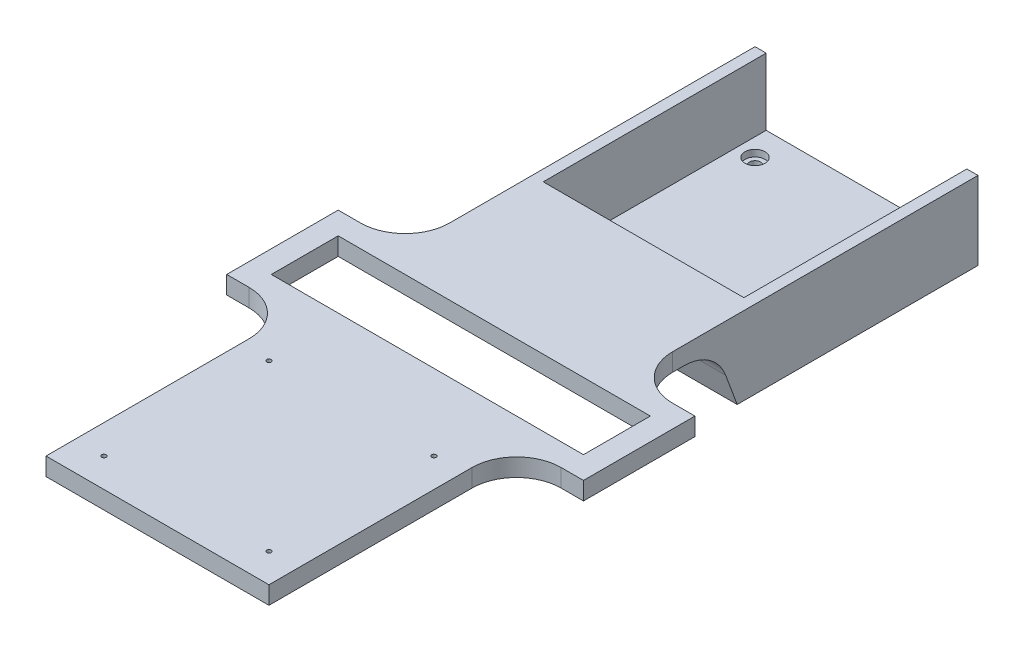
SolidWorks part; units mm, degrees
ref_plane "Front Plane" through (0, 0, 0) normal (0, 0, 1) x (1, 0, 0)
ref_plane "Top Plane" through (0, 0, 0) normal (0, 1, 0) x (1, 0, 0)
ref_plane "Right Plane" through (0, 0, 0) normal (1, 0, 0) x (0, 0, -1)
sketch "Sketch1" plane through (0, 0, 0) normal (0, 1, 0) x (1, 0, 0)
  line L0 (0, 44.3291) -> (0, -49.0863) construction
  line L1 (-50, 50) -> (50, 50)
  line L2 (-50, 50) -> (-50, -50)
  line L3 (-50, -50) -> (50, -50)
  line L4 (50, 50) -> (50, -50)
  line L5 (-50, 50) -> (50, -50) construction
  line L6 (-50, -50) -> (50, 50) construction
  line L7 (-55.6456, 0) -> (53.7715, 0) construction
  circle A0 centre (-36.95, 36.95) radius 2.5
  circle A1 centre (36.95, 36.95) radius 2.5
  circle A2 centre (36.95, -36.95) radius 2.5
  circle A3 centre (-36.95, -36.95) radius 2.5
  point P1 (0, 0)
  dimension "D1" = 73.9
  dimension "D2" = 73.9
  dimension "D4" = 5
  dimension "D3" = 100
extrude "Boss-Extrude1" add sketch "Sketch1" along normal blind 5
sketch "Sketch6" plane through (0, 0, 0) normal (0, -1, 0) x (1, 0, 0)
  line L0 (59.8047, 0) -> (-72.4197, 0) construction
  line L1 (0, 49.555) -> (0, -51.1902) construction
  circle A0 centre (-36.95, 36.95) radius 4.5
  circle A1 centre (36.95, 36.95) radius 4.5
  circle A2 centre (36.95, -36.95) radius 4.5
  circle A3 centre (-36.95, -36.95) radius 4.5
  dimension "D1" = 9
extrude "Cut-Extrude1" cut sketch "Sketch6" along normal blind 3 from surface at -5 starting at face at (36.95, 5, 39.45)
sketch "Sketch8" plane through (-50, 0, 0) normal (-1, 0, 0) x (0, 0, 1)
  line L1 (50, 0) -> (58, 0)
  line L2 (50, 0) -> (50, 35)
  line L3 (50, 35) -> (58, 35)
  line L4 (58, 0) -> (58, 35)
  dimension "D1" = 8
  dimension "D2" = 35
extrude "Boss-Extrude2" add sketch "Sketch8" against normal through all
sketch "Sketch9" plane through (0, 0, 58) normal (0, 0, 1) x (1, 0, 0)
  line L0 (50, 0) -> (50, 35) construction
  line L1 (-50, 35) -> (50, 35)
  line L2 (-50, 35) -> (-50, 27)
  line L3 (-50, 27) -> (50, 27)
  line L4 (50, 35) -> (50, 27)
  dimension "D1" = 8
extrude "Boss-Extrude3" add sketch "Sketch9" along normal blind 210
sketch "Sketch10" plane through (0, 35, 0) normal (0, 1, 0) x (1, 0, 0)
  line L0 (-50, -268) -> (-50, -50) construction
  line L1 (-80, -106.95) -> (80, -106.95)
  line L2 (-80, -106.95) -> (-80, -156.95)
  line L3 (-80, -156.95) -> (80, -156.95)
  line L4 (80, -106.95) -> (80, -156.95)
  line L5 (-80, -106.95) -> (80, -156.95) construction
  line L6 (-80, -156.95) -> (80, -106.95) construction
  line L7 (50, -268) -> (50, -50) construction
  circle A0 centre (36.95, -36.95) radius 2.5 construction
  point P0 (0, -131.95)
  point P9 (80, -66.0144)
  dimension "D1" = 30
  dimension "D2" = 30
  dimension "D3" = 50
  dimension "D4" = 70
extrude "Boss-Extrude4" add sketch "Sketch10" against normal up to surface (8 mm away) up to face at (0, 27, 163)
sketch "Sketch11" plane through (0, 35, 0) normal (0, 1, 0) x (1, 0, 0)
  line L1 (-70, -116.95) -> (70, -116.95)
  line L2 (-70, -116.95) -> (-70, -146.95)
  line L3 (-70, -146.95) -> (70, -146.95)
  line L4 (70, -116.95) -> (70, -146.95)
  line L5 (-70, -116.95) -> (70, -146.95) construction
  line L6 (-70, -146.95) -> (70, -116.95) construction
  line L8 (-80, -106.95) -> (80, -156.95) construction
  line L9 (80, -106.95) -> (-80, -156.95) construction
  point P0 (0, -131.95)
  point P7 (0, 0)
  point P14 (0, -131.95)
  dimension "D1" = 140
  dimension "D2" = 30
extrude "Cut-Extrude2" cut sketch "Sketch11" against normal up to surface (8 mm away) up to face at (0, 27, 142.3)
sketch "Sketch13" plane through (0, 35, 0) normal (0, 1, 0) x (1, 0, 0)
  line L5 (-37, -181) -> (37, -255) construction
  line L6 (-37, -255) -> (37, -181) construction
  line L7 (0, -276.3326) -> (0, -189.7195) construction
  line L12 (-28.4717, -218) -> (37, -218) construction
  circle A1 centre (-37, -181) radius 1
  circle A2 centre (37, -181) radius 1
  circle A3 centre (37, -255) radius 1
  circle A4 centre (-37, -255) radius 1
  point P0 (0, -218)
  dimension "D2" = 2
  dimension "D1" = 74
extrude "Cut-Extrude3" cut sketch "Sketch13" against normal up to surface (8 mm away) up to face at (0, 27, 131.95)
fillet "Fillet1" radius 20 4 edges at (50, 31, 156.95) (-50, 31, 156.95) (50, 31, 106.95) (-50, 31, 106.95)
sketch "Sketch14" plane through (-50, 0, 0) normal (-1, 0, 0) x (0, 0, 1)
  line L0 (58, 0) -> (58, 27)
  line L1 (58, 27) -> (68, 27)
  line L2 (86.95, 27) -> (58, 27) construction
  line L3 (68, 27) -> (58, 0)
  dimension "D1" = 10
extrude "Boss-Extrude5" add sketch "Sketch14" against normal up to surface (100 mm away) up to face at (50, 16.75, 36.2375)
fillet "Fillet3" radius 20 1 edges at (0, 27, 68)
sketch "Sketch15" plane through (0, 5, 0) normal (0, 1, 0) x (1, 0, 0)
  line L0 (-50, -50) -> (50, -50) construction
  line L1 (-50, 50) -> (-45, 50)
  line L2 (-50, 50) -> (-50, -50)
  line L3 (-50, -50) -> (-45, -50)
  line L4 (-45, 50) -> (-45, -50)
  line L6 (50, 50) -> (45, 50)
  line L7 (50, 50) -> (50, -50)
  line L8 (50, -50) -> (45, -50)
  line L9 (45, 50) -> (45, -50)
  dimension "D1" = 5
extrude "Boss-Extrude6" add sketch "Sketch15" along normal up to surface (30 mm away) up to face at (-37, 35, 254)
